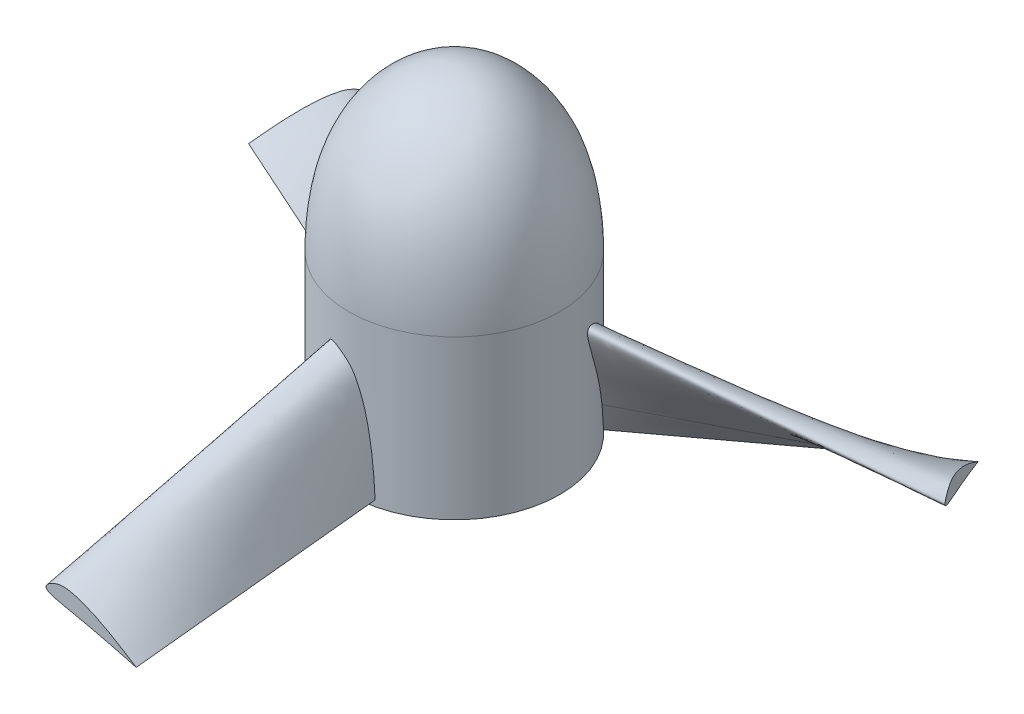
SolidWorks part; units mm, degrees
ref_plane "Front Plane" through (0, 0, 0) normal (0, 0, 1) x (1, 0, 0)
ref_plane "Top Plane" through (0, 0, 0) normal (0, 1, 0) x (1, 0, 0)
ref_plane "Right Plane" through (0, 0, 0) normal (1, 0, 0) x (0, 0, -1)
sketch "Sketch2" plane through (0, 0, 0) normal (0, 0, 1) x (1, 0, 0)
  line L0 (0, 0) -> (0, -7.62)
  line L1 (0, -7.62) -> (5.08, -7.62)
  spline S0 degree 3 poles (5.08, -7.62) (5.08, -6.593) (4.8549, -3.7737) (2.9099, -0.7789) (0.9276, 0) (0, 0) knots 0 0 0 0 0.362202 0.754656 1 1 1 1
  dimension "D1" = 5.08
  dimension "D2" = 7.62
revolve "Revolve1" add sketch "Sketch2" angle 360 about L0
sketch "Sketch3" plane through (0, -7.62, 0) normal (0, -1, 0) x (1, 0, 0)
  circle A0 centre (0, 0) radius 5.08
extrude "Boss-Extrude1" add sketch "Sketch3" along normal blind 7.62
sketch "Sketch4" plane through (0, 0, 0) normal (0, 0, 1) x (1, 0, 0)
  line L0 (0.2886, -13.0941) -> (0.6281, -14.992)
  line L1 (0.7745, -13.9072) -> (0.6281, -14.992)
  spline S0 degree 3 poles (0.2886, -13.0941) (0.2846, -13.0719) (-0.155, -10.8071) (-0.2367, -10.6648) (-1.0168, -7.0907) (0.4992, -8.0648) (0.9002, -9.4341) (1.071, -11.5551) (0.8042, -13.6866) (0.7745, -13.9072) knots 0 0 0 0 0.295732 0.489484 0.545287 0.628187 0.695896 0.795983 1 1 1 1
ref_plane "Plane1" through (0, 0, 17.78) normal (0, 0, 1) x (1, 0, 0)
sketch "Sketch5" plane through (0, 0, 17.78) normal (0, 0, 1) x (1, 0, 0)
  line L0 (1.36, -14.5525) -> (2.4782, -14.8494)
  line L1 (1.9253, -14.4945) -> (2.4782, -14.8494)
  spline S0 degree 3 poles (1.36, -14.5525) (1.3469, -14.5491) (0.0039, -14.2138) (-0.0942, -14.2222) (-2.2355, -13.7401) (-1.3214, -13.1627) (-0.4752, -13.2919) (0.7215, -13.7368) (1.813, -14.4224) (1.9253, -14.4945) knots 0 0 0 0 0.295732 0.489484 0.545287 0.628187 0.695896 0.795983 1 1 1 1
loft "Loft1" add profiles "Sketch4", "Sketch5"
pattern_circular "CirPattern1" count 3 over 360 about axis through (0, -15.24, 0) along (0, 1, 0) of "Loft1"
sketch "Sketch6" plane through (0, -15.24, 0) normal (0, -1, 0) x (1, 0, 0)
  circle A0 centre (0, 0) radius 1.27
extrude "Cut-Extrude1" cut sketch "Sketch6" against normal blind 7.62
